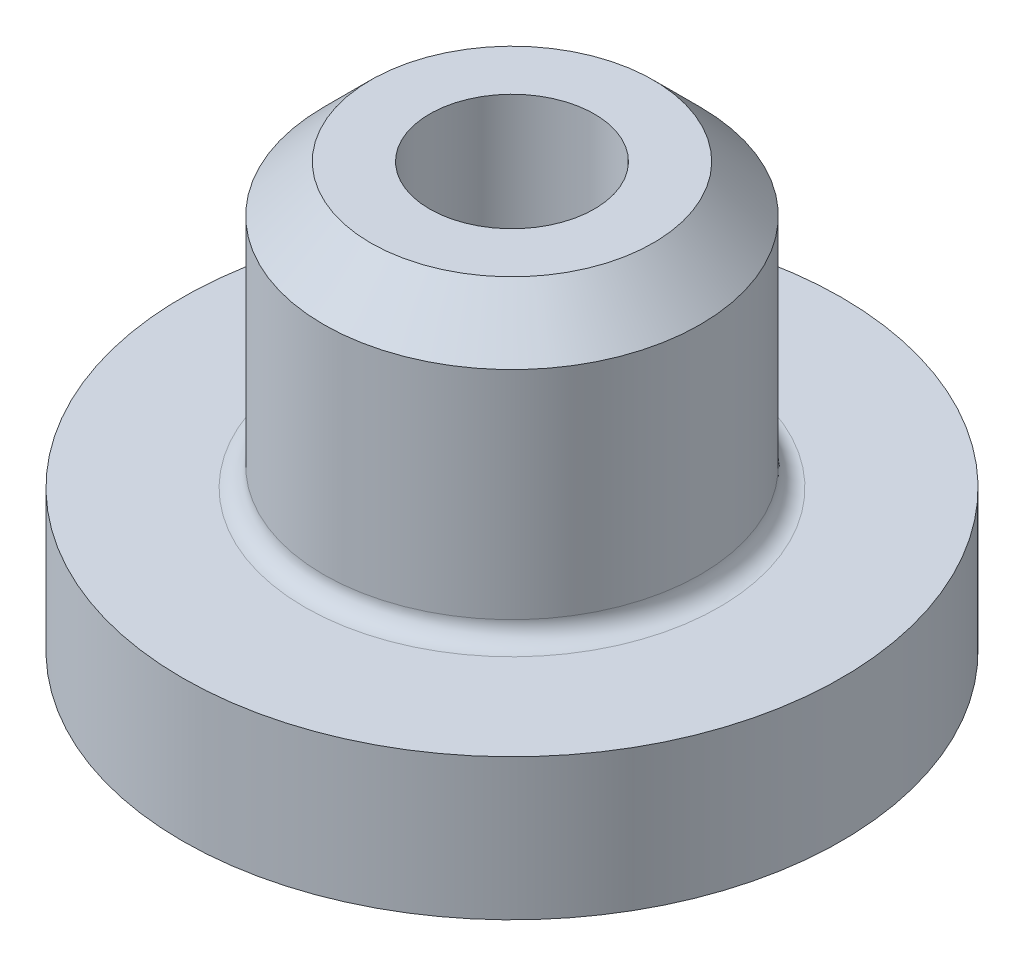
SolidWorks part; units mm, degrees
ref_plane "Front Plane" through (0, 0, 0) normal (0, 0, 1) x (1, 0, 0)
ref_plane "Top Plane" through (0, 0, 0) normal (0, 1, 0) x (1, 0, 0)
ref_plane "Right Plane" through (0, 0, 0) normal (1, 0, 0) x (0, 0, -1)
sketch "Sketch2" plane through (0, 0, 0) normal (0, 0, 1) x (1, 0, 0)
  line L0 (0, 2) -> (0, 4.5)
  line L5 (0, 4.5) -> (2, 4.5)
  line L10 (3.5, 0) -> (1.2, 0)
  line L11 (1.2, 0) -> (1.2, 2)
  line L12 (1.2, 2) -> (0, 2)
  line L13 (3.5, 0) -> (3.5, 1.5)
  line L14 (3.5, 1.5) -> (2, 1.5)
  line L15 (2, 1.5) -> (2, 4.5)
  dimension "D2" = 2
  dimension "D3" = 1.2
  dimension "D5" = 1.5
  dimension "D6" = 2
  dimension "D9" = 1.5
  dimension "D10" = 3
revolve "Revolve1" add sketch "Sketch2" angle 360 about L0
sketch "Sketch3" plane through (0, 4.5, 0) normal (0, 1, 0) x (1, 0, 0)
  circle A0 centre (0, 0) radius 0.875
  dimension "D1" = 1.75
extrude "Cut-Extrude1" cut sketch "Sketch3" against normal blind 2
chamfer "Chamfer1" distance 0.5 angle 45 1 edges at (0, 4.5, -2)
fillet "Fillet1" radius 0.2 1 edges at (0, 1.5, -2)
fillet "Fillet2" radius 0.2 2 edges at (0, 2, -1.2) (0, 2.5, 0.875)
